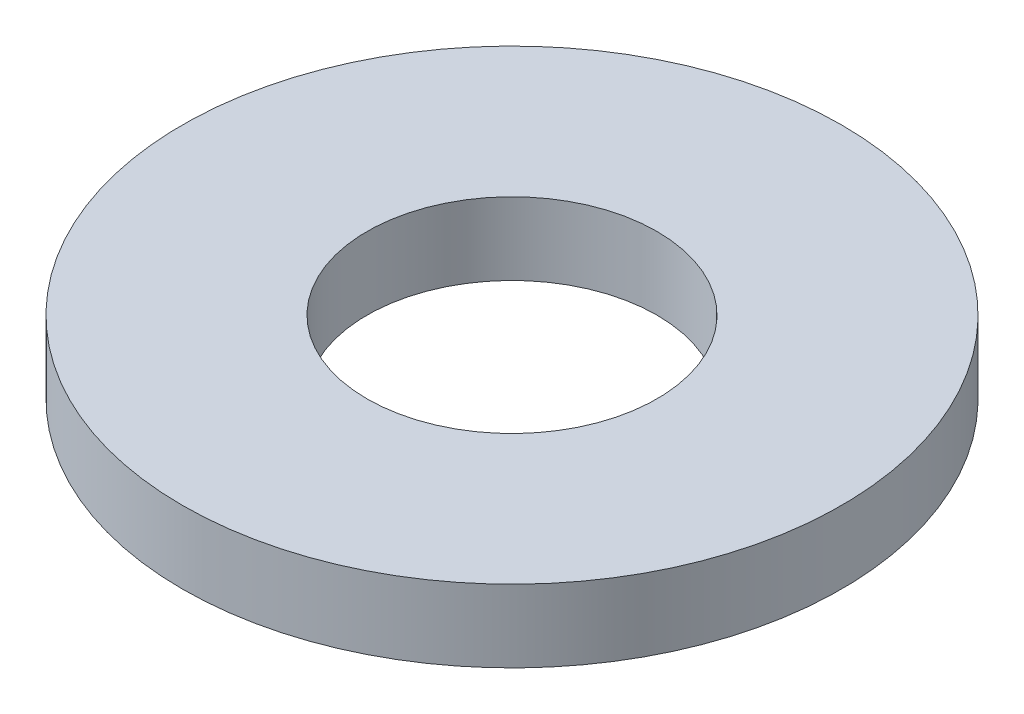
SolidWorks part; units mm, degrees
ref_plane "前视基准面" through (0, 0, 0) normal (0, 0, 1) x (1, 0, 0)
ref_plane "上视基准面" through (0, 0, 0) normal (0, 1, 0) x (1, 0, 0)
ref_plane "右视基准面" through (0, 0, 0) normal (1, 0, 0) x (0, 0, -1)
sketch "草图1" plane through (0, 0, 0) normal (0, 1, 0) x (1, 0, 0)
  circle A0 centre (0, 0) radius 2.5
  circle A1 centre (0, 0) radius 1.1
  dimension "D1" = 2.2
  dimension "D2" = 5
extrude "凸台-拉伸1" add sketch "草图1" along normal blind 0.55
